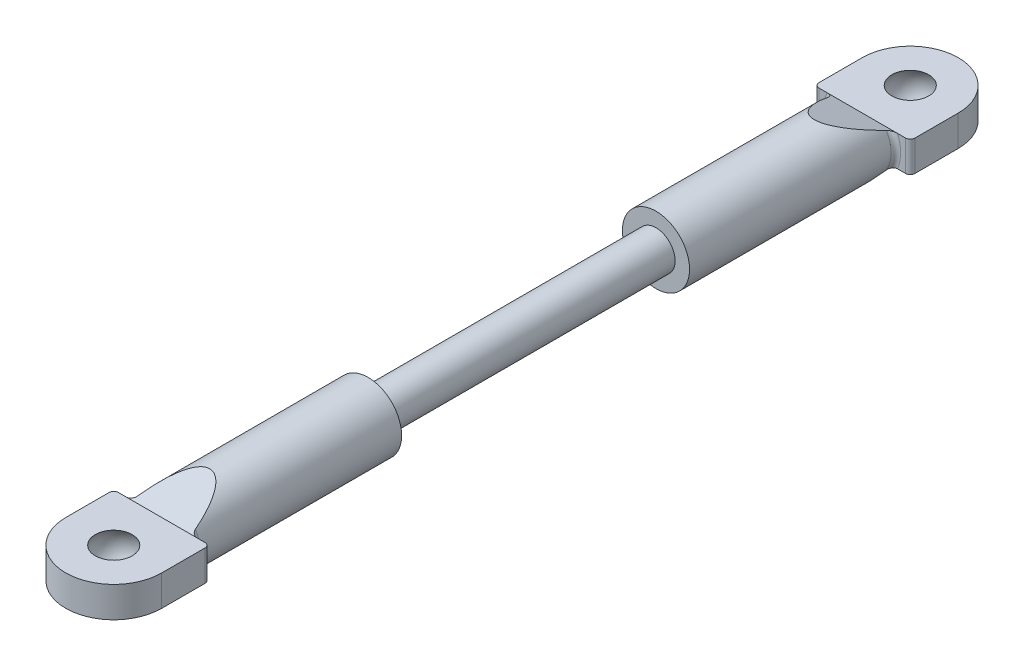
SolidWorks part; units mm, degrees
ref_plane "Front Plane" through (0, 0, 0) normal (0, 0, 1) x (1, 0, 0)
ref_plane "Top Plane" through (0, 0, 0) normal (0, 1, 0) x (1, 0, 0)
ref_plane "Right Plane" through (0, 0, 0) normal (1, 0, 0) x (0, 0, -1)
sketch "Sketch1" plane through (0, 0, 0) normal (0, 0, 1) x (1, 0, 0)
  circle A0 centre (0, 0) radius 2
  dimension "D1" = 4
extrude "Screw Section" add sketch "Sketch1" along normal blind 15 contours A0
sketch "Sketch2" plane through (0, 0, 15) normal (0, 0, 1) x (1, 0, 0)
  circle A0 centre (0, 0) radius 3.5
  dimension "D1" = 7
extrude "Bar Section" add sketch "Sketch2" along normal blind 21.5
sketch "Sketch3" plane through (0, 0, 0) normal (0, 1, 0) x (1, 0, 0)
  line L0 (5, -36.5) -> (-5, -36.5)
  line L1 (-5, -36.5) -> (-5, -41.5)
  line L2 (5, -36.5) -> (5, -41.5)
  line L3 (-3.5, -36.5) -> (3.5, -36.5) construction
  arc A0 (-5, -41.5) -> (5, -41.5) centre (0, -41.5) ccw
  point P4 (0, -46.5)
  dimension "D1" = 5
  dimension "D2" = 10
  dimension "D3" = 10
extrude "Mount Section" add sketch "Sketch3" along normal mid plane 3.2
sketch "Sketch4" plane through (0, 0, 0) normal (1, 0, 0) x (0, 0, -1)
  line L0 (-31.5, -3.5) -> (-36.5, -1.6)
  line L1 (-36.5, -3.5) -> (-15, -3.5) construction
  line L2 (-36.5, -1.6) -> (-36.5, -3.5)
  line L3 (-36.5, -1.6) -> (-36.5, -3.5) construction
  line L4 (-36.5, -3.5) -> (-31.5, -3.5)
  line L5 (-31.5, 3.5) -> (-36.5, 1.6)
  line L6 (-36.5, 3.5) -> (-36.5, 1.6) construction
  line L7 (-36.5, 3.5) -> (-31.5, 3.5)
  line L9 (-36.5, 1.6) -> (-36.5, 3.5)
  dimension "D1" = 5
  dimension "D2" = 1.9
extrude "Bar Taper" cut sketch "Sketch4" against normal through all both and the other way through all
fillet "Mount Fillet" radius 0.5 4 edges at (-5, 0, 36.5) (3.5, 0, 36.5) (-3.5, 0, 36.5) (5, 0, 36.5)
sketch "Sketch6" plane through (0, 0, 0) normal (1, 0, 0) x (0, 0, -1)
  line L0 (-41.5, 1.6) -> (-41.5, -1.6) construction
  line L1 (-46.5, -1.6) -> (-41.5, -1.6) construction
  line L2 (-41.5, 1.6) -> (-46.5, 1.6) construction
  line L4 (-43.4209, -1.6) -> (-41.5, -1.6)
  line L5 (-41.5, -1.6) -> (-41.5, 1.6)
  line L6 (-41.5, 1.6) -> (-43.4209, 1.6)
  arc A0 (-43.4209, -1.6) -> (-43.4209, 1.6) centre (-41.5, 0) cw
  dimension "D1" = 2.5
revolve "Ball Hole" cut sketch "Sketch6" angle 360 about L5
mirror "Mirror" of "Ball Hole", "Bar Section", "Bar Taper", "Mount Section", "Mount Fillet", "Screw Section"
ref_point "Point1"
ref_point "Point2"
